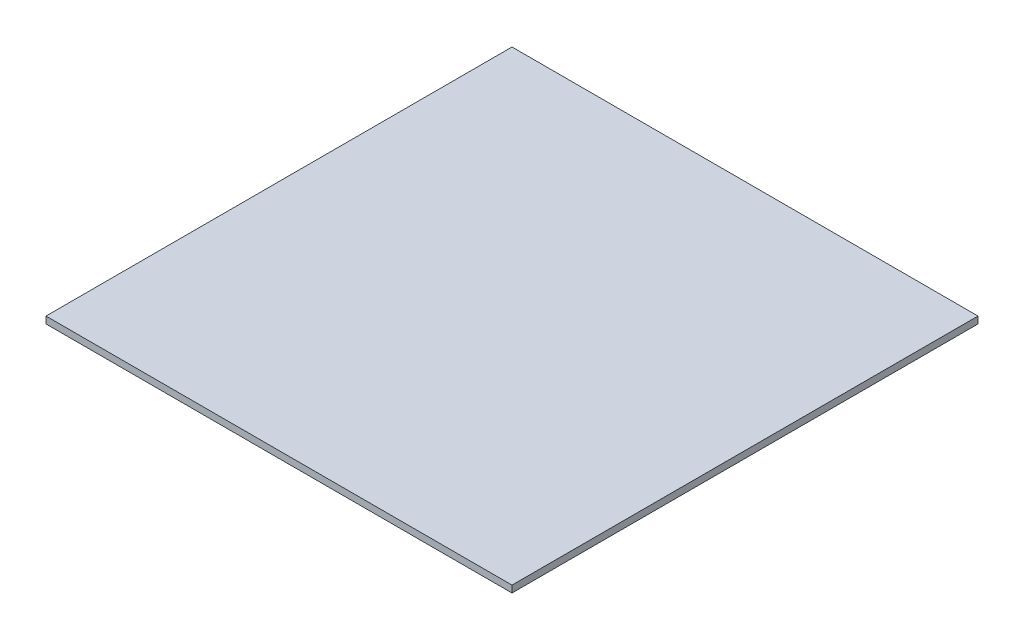
SolidWorks part; units mm, degrees
ref_plane "Front Plane" through (0, 0, 0) normal (0, 0, 1) x (1, 0, 0)
ref_plane "Top Plane" through (0, 0, 0) normal (0, 1, 0) x (1, 0, 0)
ref_plane "Right Plane" through (0, 0, 0) normal (1, 0, 0) x (0, 0, -1)
sketch "Sketch1" plane through (0, 0, 0) normal (0, 1, 0) x (1, 0, 0)
  line L1 (107.705, -107.705) -> (-107.705, -107.705)
  line L2 (107.705, -107.705) -> (107.705, 107.705)
  line L3 (107.705, 107.705) -> (-107.705, 107.705)
  line L4 (-107.705, -107.705) -> (-107.705, 107.705)
  line L5 (107.705, -107.705) -> (-107.705, 107.705) construction
  line L6 (107.705, 107.705) -> (-107.705, -107.705) construction
  point P0 (0, 0)
  point P6 (0, -107.705)
  dimension "D1" = 215.41
  dimension "D2" = 215.41
extrude "Boss-Extrude1" add sketch "Sketch1" along normal blind 3.175
